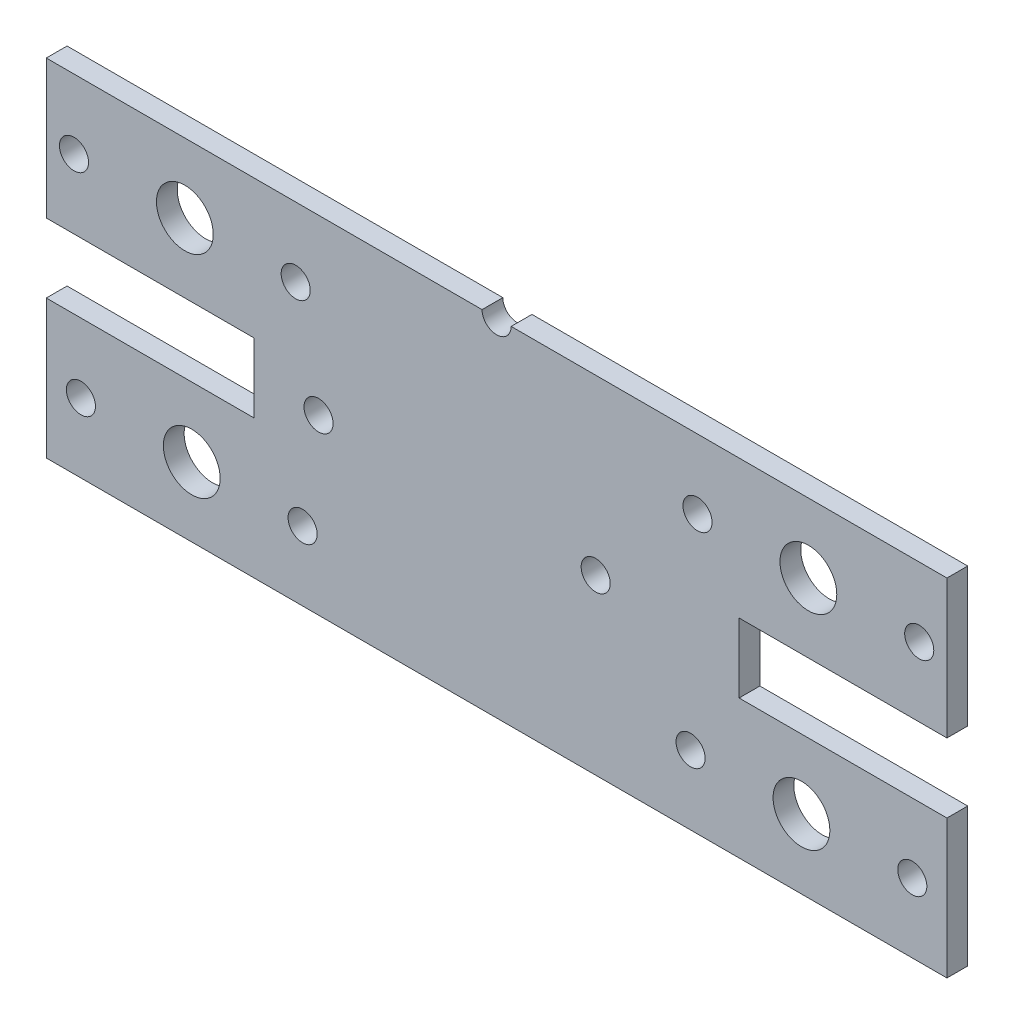
SolidWorks part; units mm, degrees
ref_plane "Plan de face" through (0, 0, 0) normal (0, 0, 1) x (1, 0, 0)
ref_plane "Plan de dessus" through (0, 0, 0) normal (0, 1, 0) x (1, 0, 0)
ref_plane "Plan de droite" through (0, 0, 0) normal (1, 0, 0) x (0, 0, -1)
sketch "Esquisse1" plane through (0, 0, 0) normal (0, 0, 1) x (1, 0, 0)
  line L1 (0, 0) -> (130, 0)
  line L2 (0, 0) -> (0, 50)
  line L3 (0, 50) -> (130, 50)
  line L4 (130, 0) -> (130, 50)
  line L7 (130, 40) -> (0, 40) construction
  line L8 (130, 10) -> (0, 10) construction
  line L10 (0, 40) -> (4, 40) construction
  line L12 (4, 40) -> (20, 40) construction
  line L13 (20, 40) -> (36, 40) construction
  line L14 (130, 40) -> (126, 40) construction
  line L15 (126, 40) -> (110, 40) construction
  line L16 (110, 40) -> (94, 40) construction
  line L17 (0, 10) -> (5, 10) construction
  line L18 (5, 10) -> (21, 10) construction
  line L19 (21, 10) -> (37, 10) construction
  line L20 (130, 10) -> (125, 10) construction
  line L21 (125, 10) -> (109, 10) construction
  line L22 (109, 10) -> (93, 10) construction
  circle A0 centre (4, 40) radius 2.1
  circle A1 centre (20, 40) radius 4.1
  circle A2 centre (36, 40) radius 2.1
  circle A3 centre (94, 40) radius 2.1
  circle A4 centre (110, 40) radius 4.1
  circle A5 centre (126, 40) radius 2.1
  circle A8 centre (5, 10) radius 2.1
  circle A9 centre (21, 10) radius 4.1
  circle A10 centre (37, 10) radius 2.1
  circle A11 centre (93, 10) radius 2.1
  circle A12 centre (109, 10) radius 4.1
  circle A13 centre (125, 10) radius 2.1
  circle A19 centre (39.3, 25) radius 2.1
  circle A20 centre (79.3, 25) radius 2.1
  point P6 (65, 0)
  point P8 (0, 25)
  point P16 (0, 0)
  point P29 (50.7, 25)
  point P30 (52.2169, 26.7706)
  point P31 (0, 0)
  dimension "D18" = 4.2
  dimension "D19" = 4.2
  dimension "D20" = 4.2
  dimension "D21" = 4.2
  dimension "D22" = 4.2
  dimension "D23" = 4.2
  dimension "D24" = 4.2
  dimension "D25" = 4.2
  dimension "D26" = 8.2
  dimension "D27" = 8.2
  dimension "D28" = 8.2
  dimension "D29" = 8.2
  dimension "D30" = 40
  dimension "D32" = 10
  dimension "D1" = 130
  dimension "D2" = 50
  dimension "D4" = 10
  dimension "D5" = 25.7
  dimension "D6" = 4
  dimension "D7" = 16
  dimension "D8" = 16
  dimension "D9" = 4
  dimension "D10" = 16
  dimension "D11" = 16
  dimension "D12" = 5
  dimension "D13" = 16
  dimension "D14" = 16
  dimension "D15" = 5
  dimension "D16" = 16
  dimension "D17" = 16
extrude "Boss.-Extru.1" add sketch "Esquisse1" along normal blind 3
sketch "Esquisse2" plane through (0, 0, 0) normal (0, 0, -1) x (-1, 0, 0)
  line L0 (0, 50) -> (0, 0) construction
  line L1 (0, 20) -> (-30, 20)
  line L2 (0, 20) -> (0, 30)
  line L3 (0, 30) -> (-30, 30)
  line L4 (-30, 20) -> (-30, 30)
  line L5 (-65, 0) -> (-65, 50) construction
  line L6 (0, 0) -> (-130, 0) construction
  line L7 (-130, 50) -> (0, 50) construction
  line L8 (-130, 30) -> (-100, 30)
  line L9 (-100, 20) -> (-100, 30)
  line L10 (-130, 20) -> (-100, 20)
  line L11 (-130, 20) -> (-130, 30)
  line L12 (-62.9, 50) -> (-67.1, 50)
  arc A0 (-67.1, 50) -> (-62.9, 50) centre (-65, 50) ccw
  point P6 (0, 25)
  point P7 (0, 25)
  dimension "D3" = 2.1
  dimension "D1" = 30
  dimension "D2" = 20
extrude "Enlèv. mat.-Extru.1" cut sketch "Esquisse2" against normal up to next
equation "\"D3@Esquisse2\"=4.2/2"
